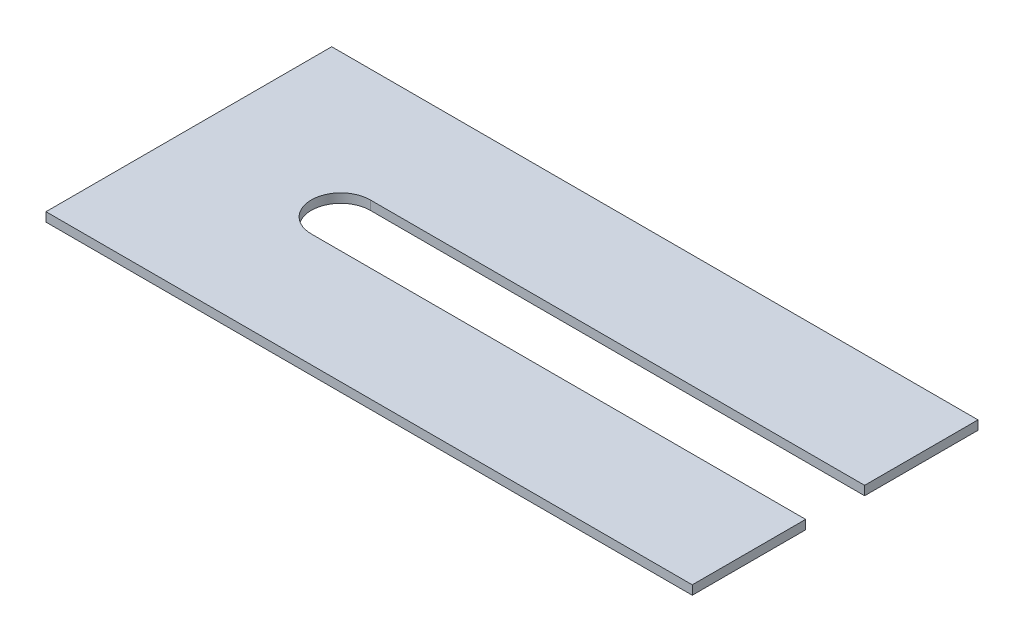
SolidWorks part; units mm, degrees
ref_plane "Front Plane" through (0, 0, 0) normal (0, 0, 1) x (1, 0, 0)
ref_plane "Top Plane" through (0, 0, 0) normal (0, 1, 0) x (1, 0, 0)
ref_plane "Right Plane" through (0, 0, 0) normal (1, 0, 0) x (0, 0, -1)
sketch "Sketch1" plane through (0, 0, 0) normal (0, 1, 0) x (1, 0, 0)
  line L0 (71.25, 15.75) -> (16.75, 15.75) construction
  line L1 (0, 0) -> (71.25, 0)
  line L2 (0, 0) -> (0, 31.5)
  line L3 (0, 31.5) -> (71.25, 31.5)
  line L4 (71.25, 0) -> (71.25, 31.5)
  line L5 (0, 0) -> (71.25, 31.5) construction
  line L6 (0, 31.5) -> (71.25, 0) construction
  line L7 (71.25, 12.5) -> (16.75, 12.5)
  line L8 (71.25, 19) -> (16.75, 19)
  line L9 (71.25, 19) -> (71.25, 12.5)
  arc A0 (71.25, 12.5) -> (71.25, 19) centre (71.25, 15.75) ccw
  arc A1 (16.75, 19) -> (16.75, 12.5) centre (16.75, 15.75) ccw
  point P4 (35.625, 15.75)
  point P8 (44, 15.75)
  point P13 (13.5, 15.75)
  dimension "D1" = 31.5
  dimension "D2" = 71.25
  dimension "D3" = 6.5
  dimension "D4" = 13.5
extrude "Boss-Extrude1" add sketch "Sketch1" along normal blind 1 contours A1 L8 L4 L3 L2 L1 L7
